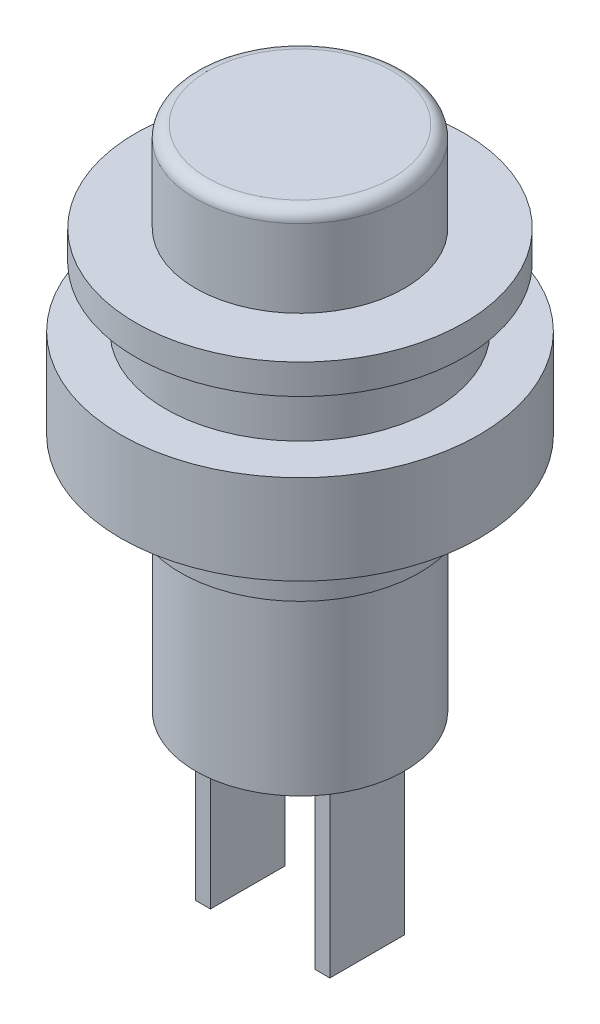
SolidWorks part; units mm, degrees
ref_plane "Front Plane" through (0, 0, 0) normal (0, 0, 1) x (1, 0, 0)
ref_plane "Top Plane" through (0, 0, 0) normal (0, 1, 0) x (1, 0, 0)
ref_plane "Right Plane" through (0, 0, 0) normal (1, 0, 0) x (0, 0, -1)
sketch "Sketch1" plane through (0, 0, 0) normal (0, 1, 0) x (1, 0, 0)
  circle A0 centre (0, 0) radius 3.5
  dimension "D1" = 7
extrude "Boss-Extrude1" add sketch "Sketch1" along normal blind 3
fillet "Fillet1" radius 0.4 1 edges at (0, 3, 3.5)
sketch "Sketch2" plane through (0, 0, 0) normal (0, -1, 0) x (1, 0, 0)
  circle A0 centre (0, 0) radius 5.5
  circle A1 centre (0, 0) radius 3.5
  circle A2 centre (0, 0) radius 3.5
  circle M2 centre (0, 0) radius 3.5
  dimension "D2" = 11
  dimension "D1" = 0
extrude "Boss-Extrude2" add sketch "Sketch2" along normal blind 1 contours M2 | A0 M2
sketch "Sketch3" plane through (0, -1, 0) normal (0, -1, 0) x (1, 0, 0)
  circle A0 centre (0, 0) radius 4.5
  dimension "D1" = 9
extrude "Boss-Extrude3" add sketch "Sketch3" along normal blind 2
sketch "Sketch4" plane through (0, -3, 0) normal (0, -1, 0) x (1, 0, 0)
  circle A0 centre (0, 0) radius 6
  circle A1 centre (0, 0) radius 4.5
  circle A2 centre (0, 0) radius 4.5
  circle M2 centre (0, 0) radius 4.5
  dimension "D2" = 12
  dimension "D1" = 0
extrude "Boss-Extrude4" add sketch "Sketch4" along normal blind 3 contours M2 | A0 M2
sketch "Sketch5" plane through (0, -6, 0) normal (0, -1, 0) x (1, 0, 0)
  circle A0 centre (0, 0) radius 4
  dimension "D1" = 8
extrude "Boss-Extrude5" add sketch "Sketch5" along normal blind 2
sketch "Sketch7" plane through (0, -8, 0) normal (0, -1, 0) x (1, 0, 0)
  circle A0 centre (0, 0) radius 3.5
  circle A1 centre (0, 0) radius 4
  circle A2 centre (0, 0) radius 4
  dimension "D2" = 7
  dimension "D1" = 0
extrude "Boss-Extrude6" add sketch "Sketch7" along normal blind 6 contours A0
sketch "Sketch8" plane through (0, -14, 0) normal (0, -1, 0) x (1, 0, 0)
  line L0 (0, 0) -> (0, 3.5)
  line L1 (0, 3.5) -> (0, -3.5)
  line L2 (0, 0) -> (-2, 0)
  line L3 (1.75, -1.25) -> (2.25, -1.25)
  line L4 (-1.75, -1.25) -> (-2.25, -1.25)
  line L5 (-1.75, -1.25) -> (-1.75, 1.25)
  line L6 (-1.75, 1.25) -> (-2.25, 1.25)
  line L7 (-2.25, -1.25) -> (-2.25, 1.25)
  line L8 (-1.75, -1.25) -> (-2.25, 1.25) construction
  line L9 (-1.75, 1.25) -> (-2.25, -1.25) construction
  line L10 (2.25, -1.25) -> (2.25, 1.25)
  line L11 (1.75, 1.25) -> (2.25, 1.25)
  line L12 (1.75, -1.25) -> (1.75, 1.25)
  circle A1 centre (0, 0) radius 3.5
  circle A2 centre (0, 0) radius 3.5
  dimension "D2" = 2
  dimension "D3" = 0.5
  dimension "D4" = 2.5
  dimension "D1" = 0
extrude "Boss-Extrude7" add sketch "Sketch8" along normal blind 6
